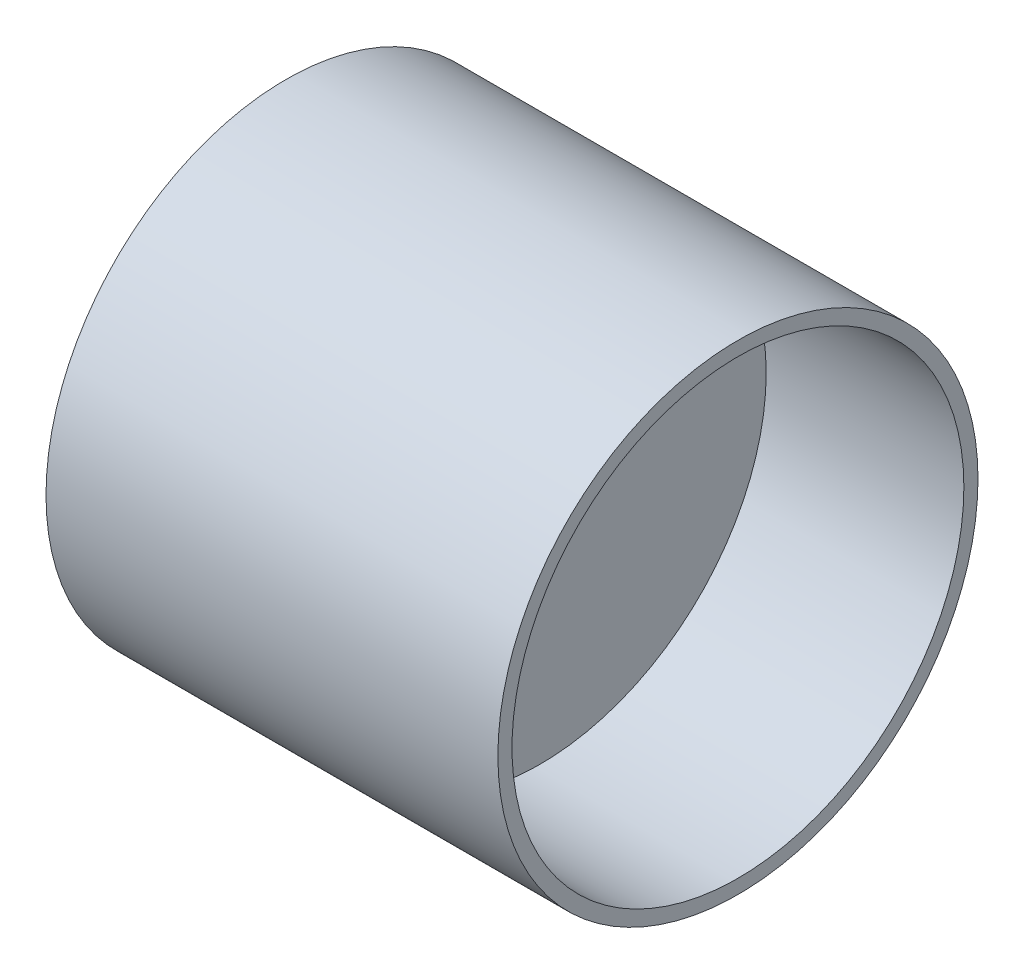
SolidWorks part; units mm, degrees
material "ABS"
ref_plane "Front Plane" through (0, 0, 0) normal (0, 0, 1) x (1, 0, 0)
ref_plane "Top Plane" through (0, 0, 0) normal (0, 1, 0) x (1, 0, 0)
ref_plane "Right Plane" through (0, 0, 0) normal (1, 0, 0) x (0, 0, -1)
sketch "Sketch1" plane through (0, 0, 0) normal (1, 0, 0) x (0, 0, -1)
  circle A0 centre (0, 0) radius 42.5
  dimension "D1" = 85
extrude "Boss-Extrude1" add sketch "Sketch1" along normal mid plane 100
ref_plane "Bolts" [suppressed] through (0, 40, 0) normal (0, 1, 0) x (1, 0, 0)
sketch "Sketch4" [suppressed] plane through (0, 40, 0) normal (0, 1, 0) x (1, 0, 0)
  line L0 (-50, 0) -> (50, 0) construction
  line L1 (50, -40) -> (50, 40) construction
  circle A0 centre (0, 0) radius 2
  circle A1 centre (30, 0) radius 2
  point P6 (0, 0)
  dimension "D3" = 4
  dimension "D1" = 30
  dimension "D2" = 50
extrude "Cut-Extrude2" [suppressed] cut sketch "Sketch4" against normal blind 15 contours A0
pattern_circular "CirPattern1" [suppressed] count 6 over 360
sketch "Sketch6" plane through (50, 0, 0) normal (1, 0, 0) x (0, 0, -1)
  circle A0 centre (0, 0) radius 40
  circle A1 centre (0, 0) radius 42.5 construction
  dimension "D1" = 2.5
extrude "Cut-Extrude6" cut sketch "Sketch6" against normal blind 35
ref_plane "Plane1" through (0, 42.5, 0) normal (0, 1, 0) x (1, 0, 0)
sketch "Sketch9" plane through (-50, 0, 0) normal (-1, 0, 0) x (0, 0, 1)
  circle A1 centre (0, 0) radius 42.5
  circle A3 centre (0, 0) radius 42.5
  dimension "D1" = 0
extrude "Cut-Extrude12" cut sketch "Sketch9" against normal blind 20
